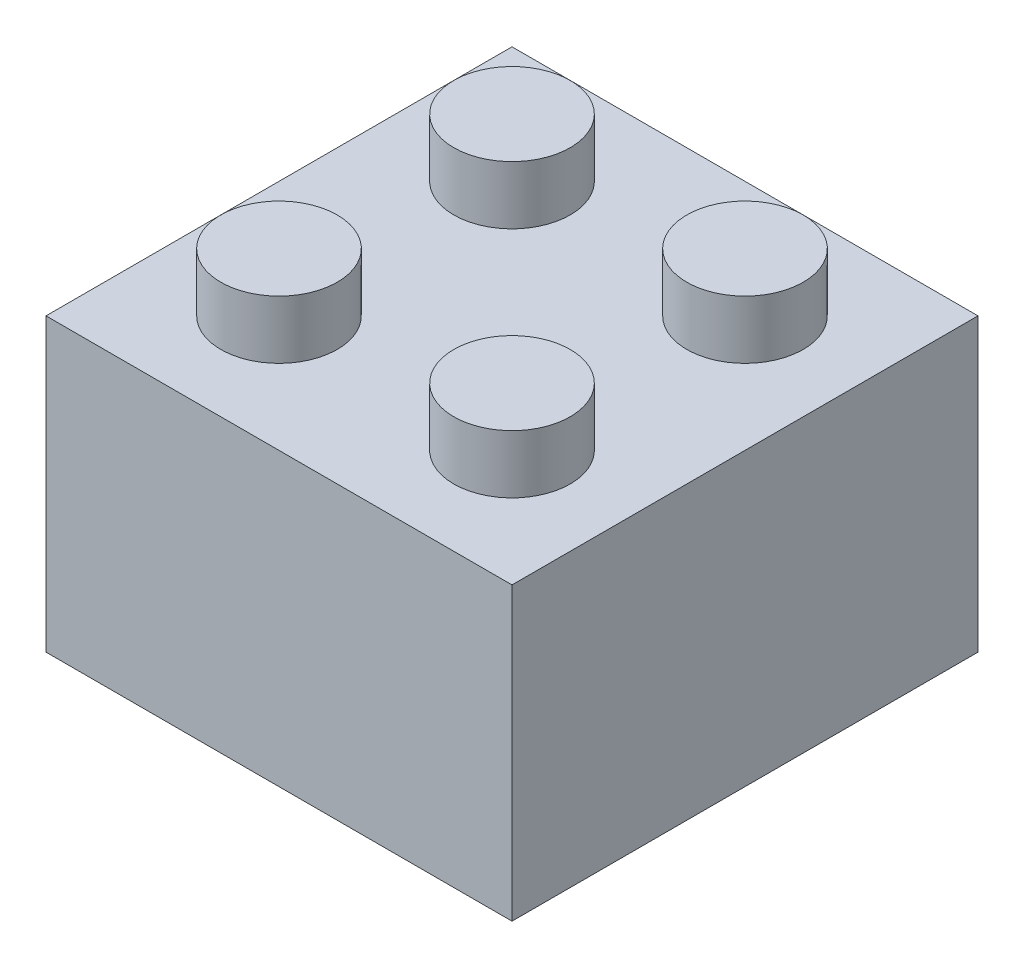
SolidWorks part; units mm, degrees
ref_plane "Front Plane" through (0, 0, 0) normal (0, 0, 1) x (1, 0, 0)
ref_plane "Top Plane" through (0, 0, 0) normal (0, 1, 0) x (1, 0, 0)
ref_plane "Right Plane" through (0, 0, 0) normal (1, 0, 0) x (0, 0, -1)
sketch "Sketch1" plane through (0, 0, 0) normal (0, 1, 0) x (1, 0, 0)
  line L1 (8, -8) -> (-8, -8)
  line L2 (8, -8) -> (8, 8)
  line L3 (8, 8) -> (-8, 8)
  line L4 (-8, -8) -> (-8, 8)
  line L5 (8, -8) -> (-8, 8) construction
  line L6 (8, 8) -> (-8, -8) construction
  point P0 (0, 0)
  dimension "D1" = 16
  dimension "D2" = 16
extrude "Boss-Extrude1" add sketch "Sketch1" along normal blind 10
sketch "Sketch2" plane through (0, 10, 0) normal (0, 1, 0) x (1, 0, 0)
  line L0 (8, 8) -> (-8, 8) construction
  line L2 (-8, 8) -> (-8, -8) construction
  line L3 (0, 8) -> (0, -8) construction
  line L4 (-8, -8) -> (8, -8) construction
  line L5 (-8, 0) -> (8, 0) construction
  line L6 (8, -8) -> (8, 8) construction
  circle A0 centre (-4, 4) radius 2
  circle A1 centre (4, 4) radius 2
  circle A2 centre (-4, -4) radius 2
  circle A3 centre (4, -4) radius 2
  dimension "D3" = 4
  dimension "D1" = 4
  dimension "D2" = 4
extrude "Boss-Extrude2" add sketch "Sketch2" along normal blind 2
shell "Shell1" thickness 1
sketch "Sketch3" plane through (0, 9, 0) normal (0, -1, 0) x (1, 0, 0)
  circle A0 centre (0, 0) radius 1.7
  circle A1 centre (0, 0) radius 2.7
  dimension "D1" = 5.4
  dimension "D2" = 3.4
extrude "Boss-Extrude3" add sketch "Sketch3" along normal blind 9 contours A0 | A1
